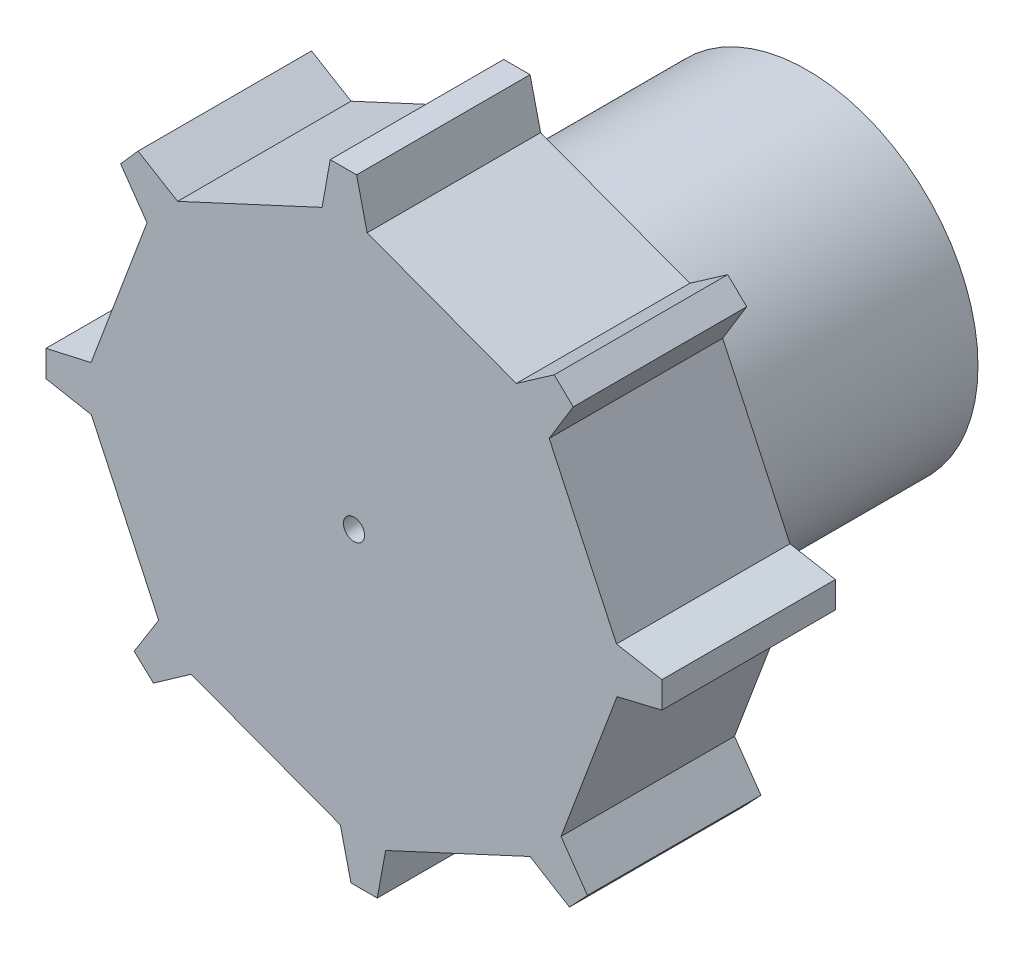
SolidWorks part; units mm, degrees
ref_plane "Front Plane" through (0, 0, 0) normal (0, 0, 1) x (1, 0, 0)
ref_plane "Top Plane" through (0, 0, 0) normal (0, 1, 0) x (1, 0, 0)
ref_plane "Right Plane" through (0, 0, 0) normal (1, 0, 0) x (0, 0, -1)
ref_plane "Plane1" through (0, 0, 0) normal (0, 0, -1) x (-1, 0, 0)
sketch "Sketch1" plane through (0, 0, 0) normal (0, 0, -1) x (-1, 0, 0)
  line L0 (22.5256, -1.7366) -> (22.5256, 0.1945)
  line L1 (22.5256, 0.1945) -> (19.2298, 0.9367)
  line L2 (19.2298, 0.9367) -> (15.1287, 11.8517)
  line L3 (15.1287, 11.8517) -> (17.0636, 14.621)
  line L4 (17.0636, 14.621) -> (15.7864, 16.0694)
  line L5 (15.7864, 16.0694) -> (12.8909, 14.3292)
  line L6 (12.8909, 14.3292) -> (2.313, 19.235)
  line L7 (2.313, 19.235) -> (1.7197, 22.5608)
  line L8 (1.7197, 22.5608) -> (-0.2115, 22.5608)
  line L9 (-0.2115, 22.5608) -> (-0.9837, 19.272)
  line L10 (-0.9837, 19.272) -> (-11.9025, 15.1806)
  line L11 (-11.9025, 15.1806) -> (-14.6739, 17.1124)
  line L12 (-14.6739, 17.1124) -> (-16.0731, 15.7814)
  line L13 (-16.0731, 15.7814) -> (-14.3088, 12.9004)
  line L14 (-14.3088, 12.9004) -> (-19.2369, 2.3329)
  line L15 (-19.2369, 2.3329) -> (-22.561, 1.7301)
  line L16 (-22.561, 1.7301) -> (-22.561, -0.201)
  line L17 (-22.561, -0.201) -> (-19.2755, -0.9874)
  line L18 (-19.2755, -0.9874) -> (-15.1744, -11.9025)
  line L19 (-15.1744, -11.9025) -> (-17.1122, -14.6697)
  line L20 (-17.1122, -14.6697) -> (-15.7881, -16.0755)
  line L21 (-15.7881, -16.0755) -> (-12.9108, -14.3052)
  line L22 (-12.9108, -14.3052) -> (-2.333, -19.211)
  line L23 (-2.333, -19.211) -> (-1.7277, -22.5347)
  line L24 (-1.7277, -22.5347) -> (0.2034, -22.5347)
  line L25 (0.2034, -22.5347) -> (0.9785, -19.2465)
  line L26 (0.9785, -19.2465) -> (11.8972, -15.1551)
  line L27 (11.8972, -15.1551) -> (14.6596, -17.0998)
  line L28 (14.6596, -17.0998) -> (16.0729, -15.7837)
  line L29 (16.0729, -15.7837) -> (14.2763, -12.9228)
  line L30 (14.2763, -12.9228) -> (19.2044, -2.3553)
  line L31 (19.2044, -2.3553) -> (22.5256, -1.7366)
extrude "Boss-Extrude1" add sketch "Sketch1" against normal blind 12.7
sketch "Sketch2" plane through (0, 0, 0) normal (0, 0, -1) x (-1, 0, 0)
  line L0 (7.602, 16.7821) -> (-7.6219, -16.7581) construction
  line L1 (12.8909, 14.3292) -> (2.313, 19.235) construction
  line L2 (-12.9108, -14.3052) -> (-2.333, -19.211) construction
  line L3 (16.7404, -7.639) -> (-16.7729, 7.6167) construction
  line L4 (14.2763, -12.9228) -> (19.2044, -2.3553) construction
  line L5 (-14.3088, 12.9004) -> (-19.2369, 2.3329) construction
  circle A0 centre (-0.0198, -0.0096) radius 0.775
  point P12 (-0.0198, -0.0096)
  dimension "D1" = 1.55
extrude "Cut-Extrude1" cut sketch "Sketch2" against normal up to next
ref_plane "Plane2" through (0, 4, 0) normal (0, 1, 0) x (1, 0, 0)
sketch "Sketch4" plane through (0, 0, 0) normal (0, 0, -1) x (-1, 0, 0)
  line L32 (19.2044, -2.3553) -> (22.5256, -1.7366)
  line L33 (22.5256, -1.7366) -> (22.5256, 0.1945)
  line L34 (22.5256, 0.1945) -> (19.2298, 0.9367)
  line L35 (19.2298, 0.9367) -> (15.1287, 11.8517)
  line L36 (15.1287, 11.8517) -> (17.0636, 14.621)
  line L37 (17.0636, 14.621) -> (15.7864, 16.0694)
  line L38 (15.7864, 16.0694) -> (12.8909, 14.3292)
  line L39 (12.8909, 14.3292) -> (2.313, 19.235)
  line L40 (2.313, 19.235) -> (1.7197, 22.5608)
  line L41 (1.7197, 22.5608) -> (-0.2115, 22.5608)
  line L42 (-0.2115, 22.5608) -> (-0.9837, 19.272)
  line L43 (-0.9837, 19.272) -> (-11.9025, 15.1806)
  line L44 (-11.9025, 15.1806) -> (-14.6739, 17.1124)
  line L45 (-14.6739, 17.1124) -> (-16.0731, 15.7814)
  line L46 (-16.0731, 15.7814) -> (-14.3088, 12.9004)
  line L47 (-14.3088, 12.9004) -> (-19.2369, 2.3329)
  line L48 (-19.2369, 2.3329) -> (-22.561, 1.7301)
  line L49 (-22.561, 1.7301) -> (-22.561, -0.201)
  line L50 (-22.561, -0.201) -> (-19.2755, -0.9874)
  line L51 (-19.2755, -0.9874) -> (-15.1744, -11.9025)
  line L52 (-15.1744, -11.9025) -> (-17.1122, -14.6697)
  line L53 (-17.1122, -14.6697) -> (-15.7881, -16.0755)
  line L54 (-15.7881, -16.0755) -> (-12.9108, -14.3052)
  line L55 (-12.9108, -14.3052) -> (-2.333, -19.211)
  line L56 (-2.333, -19.211) -> (-1.7277, -22.5347)
  line L57 (-1.7277, -22.5347) -> (0.2034, -22.5347)
  line L58 (0.2034, -22.5347) -> (0.9785, -19.2465)
  line L59 (0.9785, -19.2465) -> (11.8972, -15.1551)
  line L60 (11.8972, -15.1551) -> (14.6596, -17.0998)
  line L61 (14.6596, -17.0998) -> (16.0729, -15.7837)
  line L62 (16.0729, -15.7837) -> (14.2763, -12.9228)
  line L63 (14.2763, -12.9228) -> (19.2044, -2.3553)
  line L64 (19.2044, -2.3553) -> (22.5256, -1.7366)
  line L65 (22.5256, -1.7366) -> (22.5256, 0.1945)
  line L66 (22.5256, 0.1945) -> (19.2298, 0.9367)
  line L67 (19.2298, 0.9367) -> (15.1287, 11.8517)
  line L68 (15.1287, 11.8517) -> (17.0636, 14.621)
  line L69 (17.0636, 14.621) -> (15.7864, 16.0694)
  line L70 (15.7864, 16.0694) -> (12.8909, 14.3292)
  line L71 (12.8909, 14.3292) -> (2.313, 19.235)
  line L72 (2.313, 19.235) -> (1.7197, 22.5608)
  line L73 (1.7197, 22.5608) -> (-0.2115, 22.5608)
  line L74 (-0.2115, 22.5608) -> (-0.9837, 19.272)
  line L75 (-0.9837, 19.272) -> (-11.9025, 15.1806)
  line L76 (-11.9025, 15.1806) -> (-14.6739, 17.1124)
  line L77 (-14.6739, 17.1124) -> (-16.0731, 15.7814)
  line L78 (-16.0731, 15.7814) -> (-14.3088, 12.9004)
  line L79 (-14.3088, 12.9004) -> (-19.2369, 2.3329)
  line L80 (-19.2369, 2.3329) -> (-22.561, 1.7301)
  line L81 (-22.561, 1.7301) -> (-22.561, -0.201)
  line L82 (-22.561, -0.201) -> (-19.2755, -0.9874)
  line L83 (-19.2755, -0.9874) -> (-15.1744, -11.9025)
  line L84 (-15.1744, -11.9025) -> (-17.1122, -14.6697)
  line L85 (-17.1122, -14.6697) -> (-15.7881, -16.0755)
  line L86 (-15.7881, -16.0755) -> (-12.9108, -14.3052)
  line L87 (-12.9108, -14.3052) -> (-2.333, -19.211)
  line L88 (-2.333, -19.211) -> (-1.7277, -22.5347)
  line L89 (-1.7277, -22.5347) -> (0.2034, -22.5347)
  line L90 (0.2034, -22.5347) -> (0.9785, -19.2465)
  line L91 (0.9785, -19.2465) -> (11.8972, -15.1551)
  line L92 (11.8972, -15.1551) -> (14.6596, -17.0998)
  line L93 (14.6596, -17.0998) -> (16.0729, -15.7837)
  line L94 (16.0729, -15.7837) -> (14.2763, -12.9228)
  line L95 (14.2763, -12.9228) -> (19.2044, -2.3553)
  circle A2 centre (0, 0) radius 12.5
  circle A3 centre (0, 0) radius 2.6
  dimension "D1" = 0
extrude "Boss-Extrude3" add sketch "Sketch4" along normal offset from surface (20.5 mm away) 0.5 contours A2 A3
